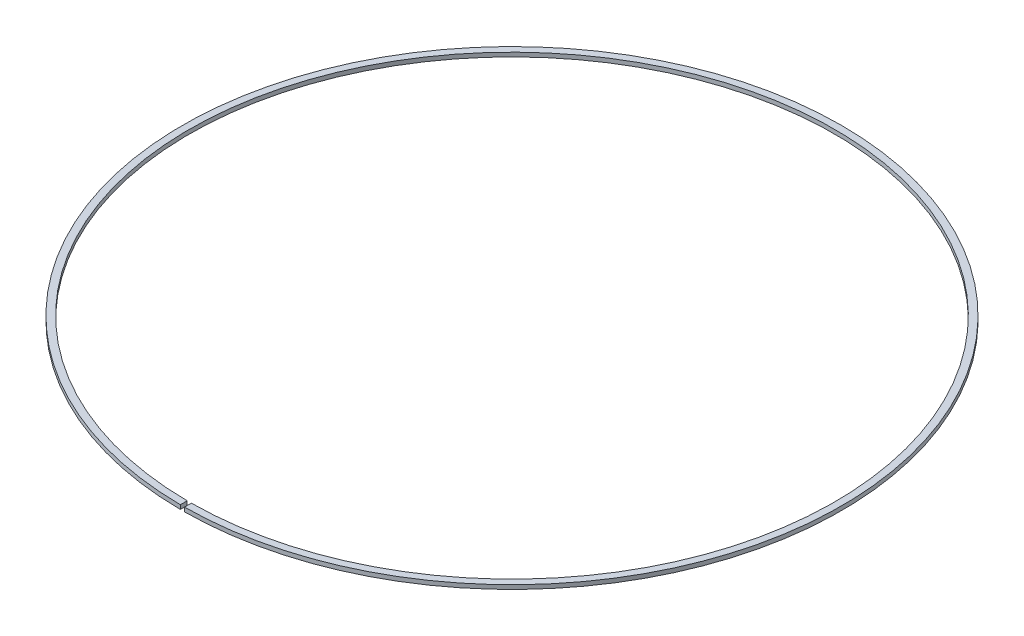
SolidWorks part; units mm, degrees
ref_plane "Front Plane" through (0, 0, 0) normal (0, 0, 1) x (1, 0, 0)
ref_plane "Top Plane" through (0, 0, 0) normal (0, 1, 0) x (1, 0, 0)
ref_plane "Right Plane" through (0, 0, 0) normal (1, 0, 0) x (0, 0, -1)
sketch "Sketch1" plane through (0, 0, 0) normal (0, 1, 0) x (1, 0, 0)
  circle A0 centre (0, 0) radius 235
  circle A1 centre (0, 0) radius 240
extrude "Boss-Extrude1" add sketch "Sketch1" along normal blind 3
sketch "Sketch2" plane through (0, 3, 0) normal (0, 1, 0) x (1, 0, 0)
  line L0 (0, 240) -> (0, -240) construction
  line L1 (-240, 0) -> (240, 0) construction
  line L2 (-1.5, -234.0712) -> (-1.5, -240.6005)
  line L3 (-1.5, -234.0712) -> (1.5, -234.0712)
  line L9 (-1.5, -240.6005) -> (1.5, -240.6005)
  line L10 (1.5, -240.6005) -> (1.5, -234.0712)
  circle A0 centre (0, 0) radius 240 construction
  point P7 (0, 0)
extrude "Cut-Extrude1" cut sketch "Sketch2" against normal blind 3
